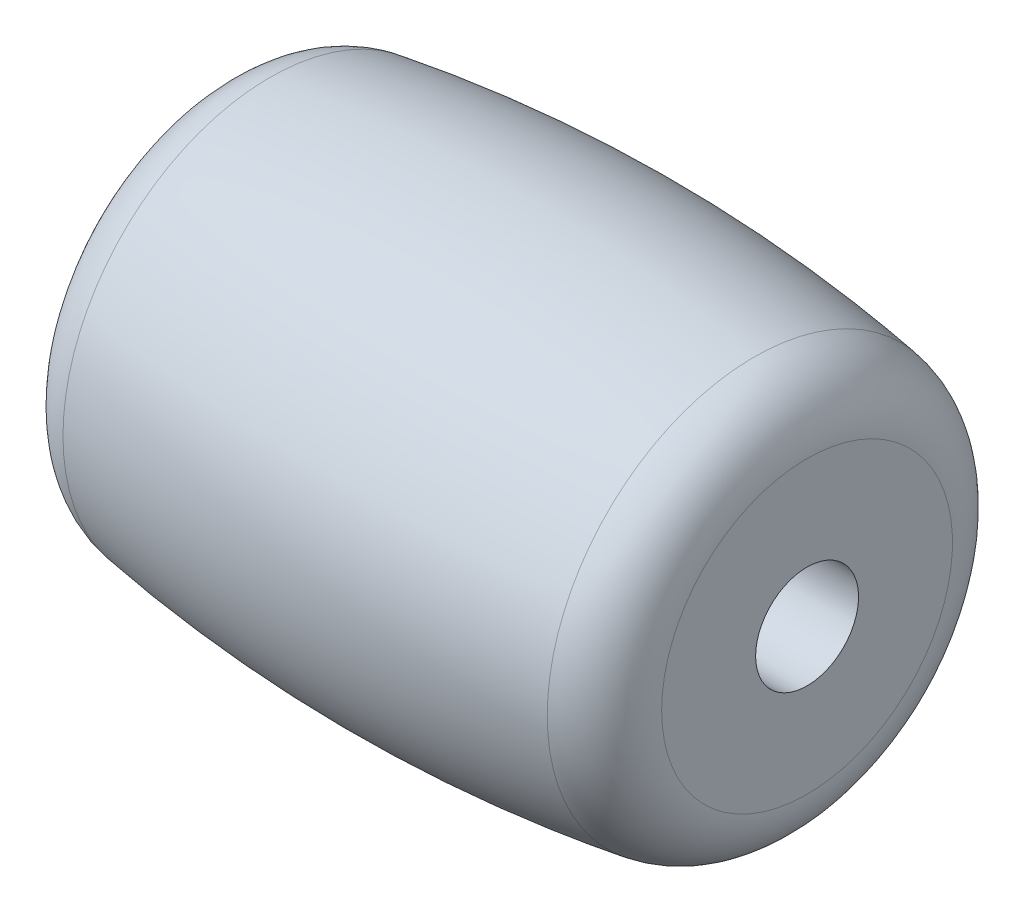
SolidWorks part; units mm, degrees
material "NEOPRENE"
ref_plane "Front Plane" through (0, 0, 0) normal (0, 0, 1) x (1, 0, 0)
ref_plane "Top Plane" through (0, 0, 0) normal (0, 1, 0) x (1, 0, 0)
ref_plane "Right Plane" through (0, 0, 0) normal (1, 0, 0) x (0, 0, -1)
sketch "Sketch1" plane through (0, 0, 0) normal (0, 0, 1) x (1, 0, 0)
  line L0 (0, 0) -> (63.6356, 0) construction
  line L1 (0, 0) -> (0, -43.561) construction
  line L2 (-9.4615, 1.651) -> (9.4615, 1.651)
  line L3 (-9.4615, 1.651) -> (-9.4615, 4.6652)
  line L4 (9.4615, 1.651) -> (9.4615, 4.6652)
  arc A0 (7.7673, 6.6417) -> (-7.7673, 6.6417) centre (0, -43.561) ccw
  arc A1 (9.4615, 4.6652) -> (7.7673, 6.6417) centre (7.4615, 4.6652) ccw
  arc A2 (-9.4615, 4.6652) -> (-7.7673, 6.6417) centre (-7.4615, 4.6652) cw
  point P7 (0, 1.651)
  dimension "D2" = 101.6
  dimension "D5" = 2
  dimension "D1" = 43.561
  dimension "D3" = 18.923
  dimension "D4" = 3.302
revolve "Revolve1" add sketch "Sketch1" angle 360 about L0
